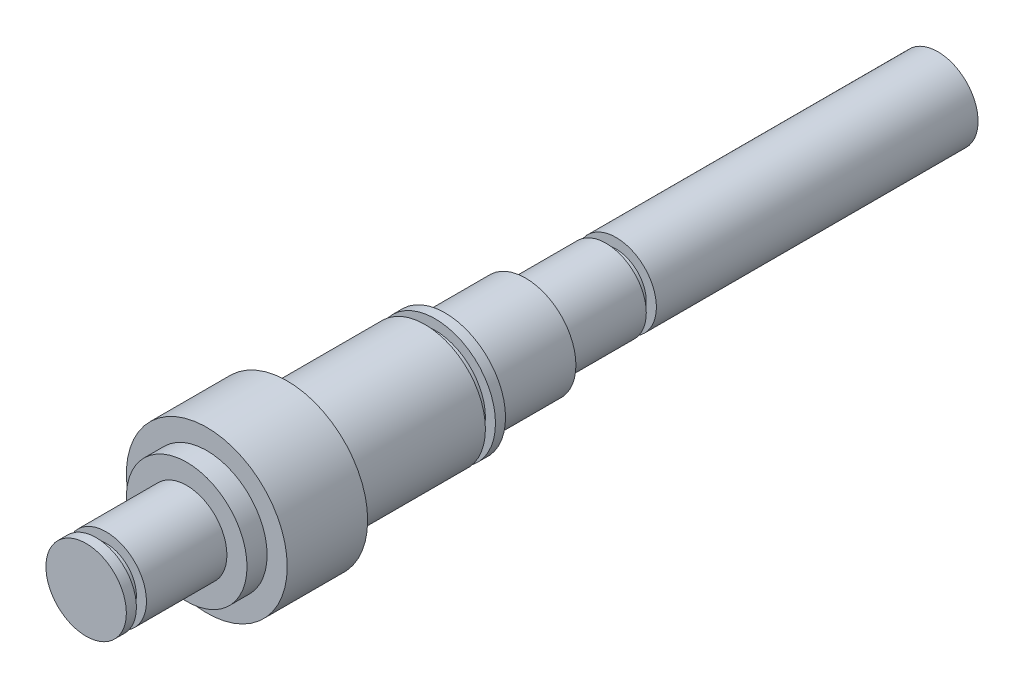
SolidWorks part; units mm, degrees
ref_plane "Front Plane" through (0, 0, 0) normal (0, 0, 1) x (1, 0, 0)
ref_plane "Top Plane" through (0, 0, 0) normal (0, 1, 0) x (1, 0, 0)
ref_plane "Right Plane" through (0, 0, 0) normal (1, 0, 0) x (0, 0, -1)
sketch "Sketch2" plane through (0, 0, 0) normal (0, 0, 1) x (1, 0, 0)
  circle A0 centre (0, 0) radius 12.7
  dimension "D1" = 25.4
extrude "Boss-Extrude1" add sketch "Sketch2" along normal blind 25.4
sketch "Sketch3" plane through (0, 0, 25.4) normal (0, 0, 1) x (1, 0, 0)
  circle A0 centre (0, 0) radius 15.875
  dimension "D1" = 31.75
extrude "Boss-Extrude2" add sketch "Sketch3" along normal blind 25.4
sketch "Sketch4" plane through (0, 0, 50.8) normal (0, 0, 1) x (1, 0, 0)
  circle A0 centre (0, 0) radius 19.05
  dimension "D1" = 38.1
extrude "Boss-Extrude3" add sketch "Sketch4" along normal blind 3.175
sketch "Sketch5" plane through (0, 0, 53.975) normal (0, 0, 1) x (1, 0, 0)
  circle A0 centre (0, 0) radius 15.875
  circle A1 centre (0, 0) radius 19.05 construction
  dimension "D1" = 3.175
extrude "Boss-Extrude4" add sketch "Sketch5" along normal blind 3.175
sketch "Sketch6" plane through (0, 0, 57.15) normal (0, 0, 1) x (1, 0, 0)
  circle A0 centre (0, 0) radius 19.05
  circle A1 centre (0, 0) radius 15.875 construction
  dimension "D1" = 3.175
extrude "Boss-Extrude5" add sketch "Sketch6" along normal blind 43.5356
sketch "Sketch7" plane through (0, 0, 100.6856) normal (0, 0, 1) x (1, 0, 0)
  circle A0 centre (0, 0) radius 25.4
  dimension "D1" = 50.8
extrude "Boss-Extrude6" add sketch "Sketch7" along normal blind 25.4
sketch "Sketch8" plane through (0, 0, 126.0856) normal (0, 0, 1) x (1, 0, 0)
  circle A0 centre (0, 0) radius 19.05
  dimension "D1" = 38.1
extrude "Boss-Extrude7" add sketch "Sketch8" along normal blind 6.35
sketch "Sketch9" plane through (0, 0, 132.4356) normal (0, 0, 1) x (1, 0, 0)
  circle A0 centre (0, 0) radius 12.7
  dimension "D1" = 25.4
extrude "Boss-Extrude8" add sketch "Sketch9" along normal blind 25.4
ref_plane "Plane4" through (0, -19.05, 0) normal (0, -1, 0) x (-1, 0, 0)
sketch "Sketch10" plane through (0, -19.05, 0) normal (0, -1, 0) x (-1, 0, 0)
  line L0 (0, -69.3928) -> (0, -88.4428) construction
  line L3 (3.175, -69.3928) -> (3.175, -88.4428)
  line L4 (-3.175, -69.3928) -> (-3.175, -88.4428)
  line L5 (-19.05, -57.15) -> (-19.05, -100.6856) construction
  arc A2 (3.175, -69.3928) -> (-3.175, -69.3928) centre (0, -69.3928) ccw
  arc A3 (-3.175, -88.4428) -> (3.175, -88.4428) centre (0, -88.4428) ccw
  point P3 (0, -78.9178)
  point P8 (0, -66.2178)
  point P9 (0, -91.6178)
  point P15 (-19.05, -78.9178)
  dimension "D2" = 3.175
  dimension "D1" = 25.4
extrude "Cut-Extrude1" cut sketch "Sketch10" against normal blind 3.175
sketch "Sketch11" plane through (0, 0, 0) normal (0, 0, -1) x (-1, 0, 0)
  circle A0 centre (0, 0) radius 9.525
  circle A1 centre (0, 0) radius 12.7 construction
  dimension "D1" = 3.175
extrude "Boss-Extrude9" add sketch "Sketch11" along normal blind 3.175
sketch "Sketch12" plane through (0, 0, -3.175) normal (0, 0, -1) x (-1, 0, 0)
  circle A0 centre (0, 0) radius 12.7
  circle A1 centre (0, 0) radius 9.525 construction
  dimension "D1" = 3.175
extrude "Boss-Extrude10" add sketch "Sketch12" along normal blind 101.6
sketch "Sketch13" plane through (0, 0, 157.8356) normal (0, 0, 1) x (1, 0, 0)
  circle A0 centre (0, 0) radius 9.525
  circle A1 centre (0, 0) radius 12.7 construction
  dimension "D1" = 3.175
extrude "Boss-Extrude11" add sketch "Sketch13" along normal blind 3.175
sketch "Sketch14" plane through (0, 0, 161.0106) normal (0, 0, 1) x (1, 0, 0)
  circle A0 centre (0, 0) radius 12.7
  circle A1 centre (0, 0) radius 9.525 construction
  dimension "D1" = 3.175
extrude "Boss-Extrude12" add sketch "Sketch14" along normal blind 3.175
